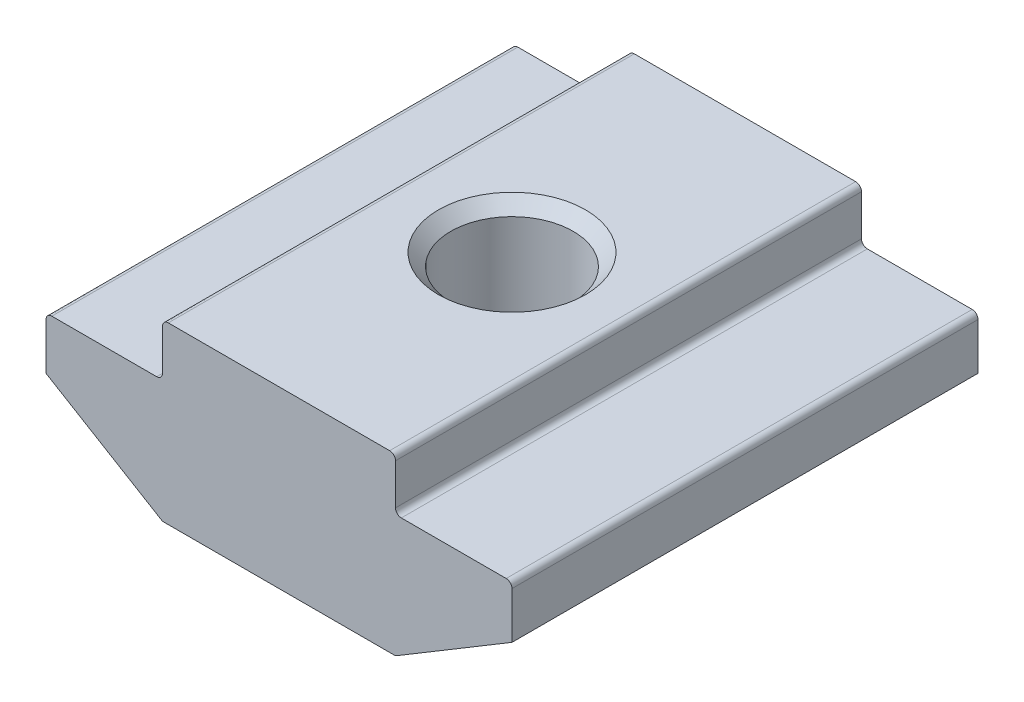
SolidWorks part; units mm, degrees
ref_plane "Спереди" through (0, 0, 0) normal (0, 0, 1) x (1, 0, 0)
ref_plane "Сверху" through (0, 0, 0) normal (0, 1, 0) x (1, 0, 0)
ref_plane "Справа" through (0, 0, 0) normal (1, 0, 0) x (0, 0, -1)
sketch "Эскиз1" plane through (0, 0, 0) normal (0, 0, 1) x (1, 0, 0)
  line L0 (4, 0) -> (-4, 0)
  line L1 (-4, 0) -> (-4, -1.8)
  line L2 (-4, -1.8) -> (-8, -1.8)
  line L3 (-8, -1.8) -> (-8, -3.6)
  line L4 (-8, -3.6) -> (-4, -6)
  line L5 (-4, -6) -> (4, -6)
  line L6 (0, -6) -> (0, 0) construction
  line L7 (8, -3.6) -> (4, -6)
  line L8 (8, -1.8) -> (8, -3.6)
  line L9 (4, -1.8) -> (8, -1.8)
  line L10 (4, 0) -> (4, -1.8)
  point P3 (-4, -0.9)
  point P9 (-2.7421, -5)
  point P10 (-5, -1.6182)
  dimension "D1" = 8
  dimension "D2" = 16
  dimension "D4" = 6
  dimension "D5" = 4.2
extrude "Бобышка-Вытянуть1" add sketch "Эскиз1" along normal mid plane 16
hole_wizard "Отверстие обработанное метчиком M52" positions "Эскиз2" profile "Эскиз4" tap size "M5" standard "ISO" end condition through all
sketch "Эскиз2" plane through (0, 0, 0) normal (0, 1, 0) x (1, 0, 0)
  point P0 (0, 0)
sketch "Эскиз4" plane through (0, 0, 0) normal (1, 0, 0) x (0, 0, 1)
  line L0 (0, 0) -> (0, 6)
  line L1 (0, 6) -> (2.525, 6)
  line L2 (2.1, 5.575) -> (2.1, 0.425)
  line L3 (2.1, 0.425) -> (2.525, 0)
  line L5 (2.525, 0) -> (0, 0)
  line L6 (-2.1, 0.425) -> (-2.525, 0) construction
  line L7 (2.525, 6) -> (2.1, 5.575)
  line L8 (-2.525, 6) -> (-2.1, 5.575) construction
  line L11 (0, -6.35) -> (0, 107.95) construction
  dimension "Диаметр проходного сверла" = 4.2
  dimension "Глубина проходного сверла" = 6
  dimension "Диаметр передней зенковки" = 5.05
  dimension "Угол передней зенковки" = 90
  dimension "Диаметр задней зенковки" = 5.05
  dimension "Угол задней зенковки" = 90
cosmetic thread "Отверстие резьбы1" parameters "D2"=5
fillet "Скругление1" radius 0.2 8 edges at (4, -6, 0) (-4, -6, 0) (8, -1.8, 0) (4, -1.8, 0) (4, 0, 0) (-4, 0, 0) (-8, -1.8, 0) (-4, -1.8, 0)
